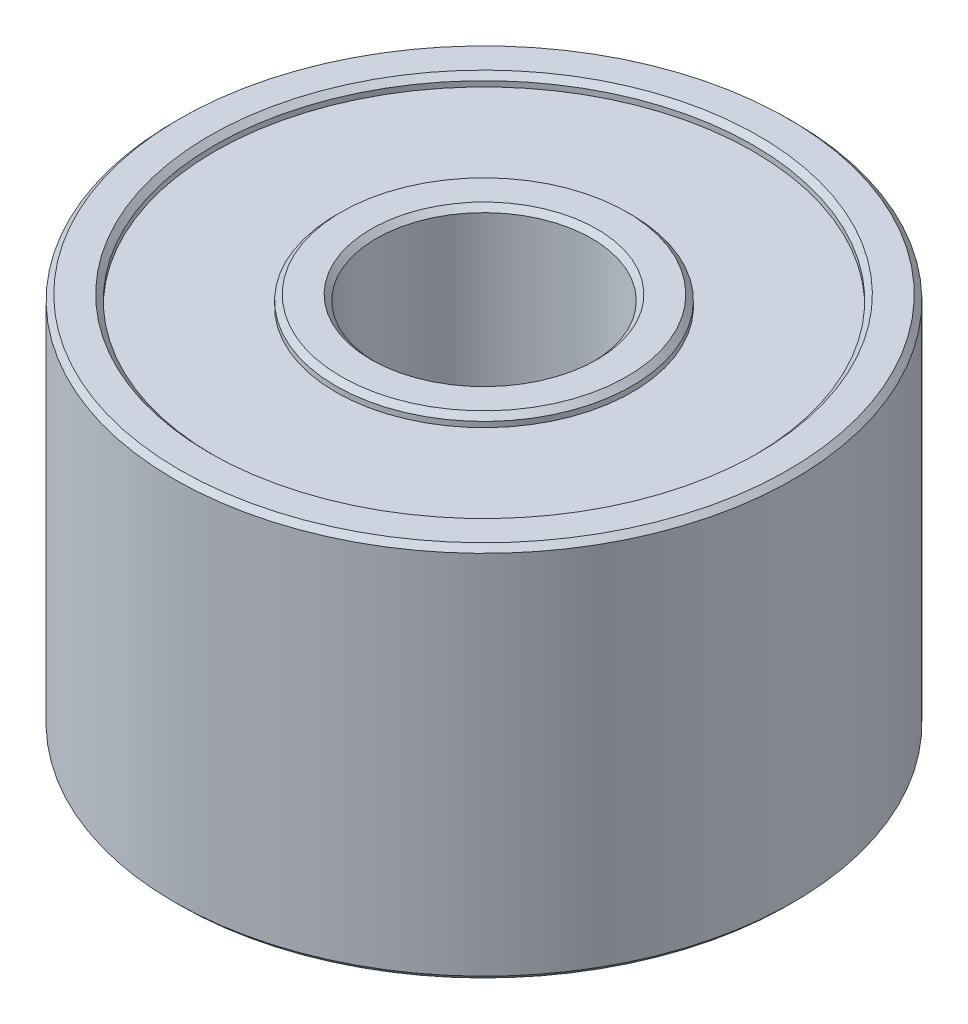
SolidWorks part; units mm, degrees
ref_plane "Front" through (0, 0, 0) normal (0, 0, 1) x (1, 0, 0)
ref_plane "Top" through (0, 0, 0) normal (0, 1, 0) x (1, 0, 0)
ref_plane "Right" through (0, 0, 0) normal (1, 0, 0) x (0, 0, -1)
sketch "草图1" plane through (0, 0, 0) normal (0, 1, 0) x (1, 0, 0)
  circle A0 centre (0, 0) radius 11.5
  dimension "D1" = 23
extrude "凸台-拉伸1" add sketch "草图1" along normal blind 14
sketch "草图2" plane through (0, 14, 0) normal (0, 1, 0) x (1, 0, 0)
  circle A0 centre (0, 0) radius 4
  dimension "D1" = 8
extrude "切除-拉伸1" cut sketch "草图2" against normal blind 24
sketch "草图3" plane through (0, 14, 0) normal (0, 1, 0) x (1, 0, 0)
  circle A0 centre (0, 0) radius 5.5
  circle A1 centre (0, 0) radius 10
  circle A2 centre (0, 0) radius 4 construction
  circle A3 centre (0, 0) radius 11.5 construction
  point P5 (0, 0)
  dimension "D1" = 1.5
  dimension "D2" = 1.5
extrude "切除-拉伸2" cut sketch "草图3" against normal blind 0.4
sketch "草图4" plane through (0, 0, 0) normal (0, -1, 0) x (1, 0, 0)
  circle A0 centre (0, 0) radius 5.5
  circle A1 centre (0, 0) radius 10
  circle A2 centre (0, 0) radius 4 construction
  circle A3 centre (0, 0) radius 11.5 construction
  point P3 (0, 0)
  dimension "D1" = 1.5
  dimension "D2" = 1.5
extrude "切除-拉伸3" cut sketch "草图4" against normal blind 0.4
chamfer "倒角1" distance 0.2 angle 45 8 edges at (0, 14, 11.5) (0, 14, 10) (0, 14, 5.5) (0, 14, 4) (0, 0, 11.5) (0, 0, -10) (0, 0, -5.5) (0, 0, 4)
